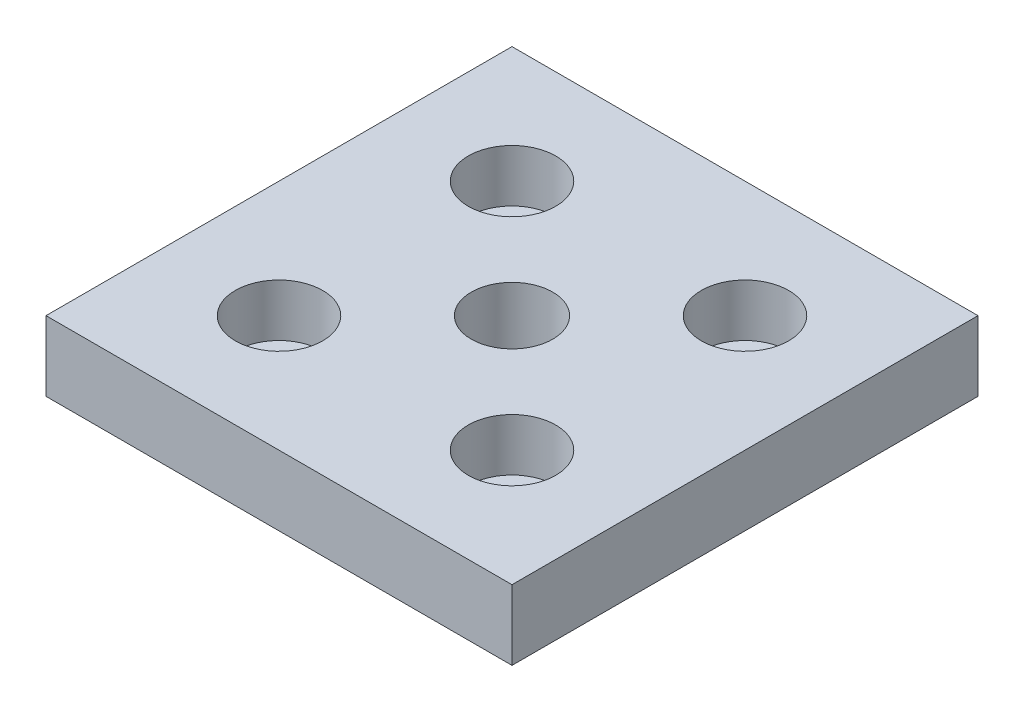
SolidWorks part; units mm, degrees
material "Алюминиевый сплав"
ref_plane "Спереди" through (0, 0, 0) normal (0, 0, 1) x (1, 0, 0)
ref_plane "Сверху" through (0, 0, 0) normal (0, 1, 0) x (1, 0, 0)
ref_plane "Справа" through (0, 0, 0) normal (1, 0, 0) x (0, 0, -1)
sketch "Эскиз1" plane through (0, 0, 0) normal (0, 1, 0) x (1, 0, 0)
  line L1 (-40, -40) -> (40, -40)
  line L2 (-40, -40) -> (-40, 40)
  line L3 (-40, 40) -> (40, 40)
  line L4 (40, -40) -> (40, 40)
  line L5 (-40, -40) -> (40, 40) construction
  line L6 (-40, 40) -> (40, -40) construction
  point P0 (0, 0)
  dimension "D1" = 80
extrude "Бобышка-Вытянуть1" add sketch "Эскиз1" along normal blind 12
hole_wizard "Отверстие обработанное метчиком M161" positions "Эскиз6" profile "Эскиз7" tap size "M16" standard "ISO" end condition up to next
sketch "Эскиз6" plane through (0, 12, 0) normal (0, 1, 0) x (1, 0, 0)
  point P0 (0, 0)
sketch "Эскиз7" plane through (0, 12, 0) normal (1, 0, 0) x (0, 0, 1)
  line L0 (0, 0) -> (0, 12)
  line L1 (0, 12) -> (7, 12)
  line L2 (7, 12) -> (7, 0)
  line L5 (7, 0) -> (0, 0)
  line L11 (0, -6.35) -> (0, 107.95) construction
  dimension "Диаметр проходного сверла" = 14
  dimension "Глубина проходного сверла" = 12
cosmetic thread "Отверстие резьбы2" parameters "D2"=16
sketch "Эскиз12" plane through (0, 12, 0) normal (0, 1, 0) x (1, 0, 0)
  line L1 (20, -20) -> (-20, -20) construction
  line L2 (20, -20) -> (20, 20) construction
  line L3 (20, 20) -> (-20, 20) construction
  line L4 (-20, -20) -> (-20, 20) construction
  line L5 (20, -20) -> (-20, 20) construction
  line L6 (20, 20) -> (-20, -20) construction
  circle A0 centre (-20, 20) radius 4.5
  circle A1 centre (20, 20) radius 4.5
  circle A2 centre (20, -20) radius 4.5
  circle A3 centre (-20, -20) radius 4.5
  point P0 (0, 0)
  dimension "D2" = 9
  dimension "D1" = 40
extrude "Вырез-Вытянуть1" cut sketch "Эскиз12" against normal through all
sketch "Эскиз13" plane through (0, 12, 0) normal (0, 1, 0) x (1, 0, 0)
  circle A0 centre (-20, 20) radius 7.5
  circle A1 centre (20, 20) radius 7.5
  circle A2 centre (20, -20) radius 7.5
  circle A3 centre (-20, -20) radius 7.5
  dimension "D1" = 15
extrude "Вырез-Вытянуть2" cut sketch "Эскиз13" against normal blind 9
